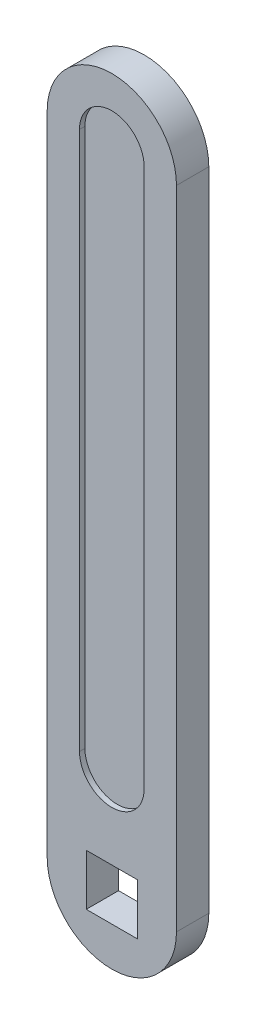
SolidWorks part; units mm, degrees
material "普通碳钢"
ref_plane "前视基准面" through (0, 0, 0) normal (0, 0, 1) x (1, 0, 0)
ref_plane "上视基准面" through (0, 0, 0) normal (0, 1, 0) x (1, 0, 0)
ref_plane "右视基准面" through (0, 0, 0) normal (1, 0, 0) x (0, 0, -1)
sketch "草图1" plane through (0, 0, 0) normal (0, 0, 1) x (1, 0, 0)
  line L0 (0, 0) -> (0, 120) construction
  line L1 (4.75, 4.75) -> (-4.75, 4.75)
  line L2 (4.75, 4.75) -> (4.75, -4.75)
  line L3 (4.75, -4.75) -> (-4.75, -4.75)
  line L4 (-4.75, 4.75) -> (-4.75, -4.75)
  line L5 (4.75, 4.75) -> (-4.75, -4.75) construction
  line L6 (4.75, -4.75) -> (-4.75, 4.75) construction
  line L7 (-12, 0) -> (-12, 120)
  line L8 (12, 0) -> (12, 120)
  arc A0 (-12, 0) -> (12, 0) centre (0, 0) ccw
  arc A1 (12, 120) -> (-12, 120) centre (0, 120) ccw
  point P0 (0, 0)
  point P8 (0, 60)
  dimension "D3" = 12
  dimension "D1" = 9.5
  dimension "D2" = 9.5
  dimension "D4" = 120
extrude "凸台-拉伸1" add sketch "草图1" along normal mid plane 6
sketch "草图2" plane through (0, 0, 3) normal (0, 0, 1) x (1, 0, 0)
  line L0 (0, 20) -> (0, 120) construction
  line L1 (-6, 20) -> (-6, 120)
  line L2 (6, 20) -> (6, 120)
  arc A0 (-6, 20) -> (6, 20) centre (0, 20) ccw
  arc A1 (6, 120) -> (-6, 120) centre (0, 120) ccw
  point P3 (0, 70)
  dimension "D1" = 6
  dimension "D2" = 100
extrude "切除-拉伸1" cut sketch "草图2" against normal blind 1
mirror "镜向1" about plane through (0, 0, 0) normal (0, 0, 1) of "切除-拉伸1"
equation "\"9。5\"=15.0209"
